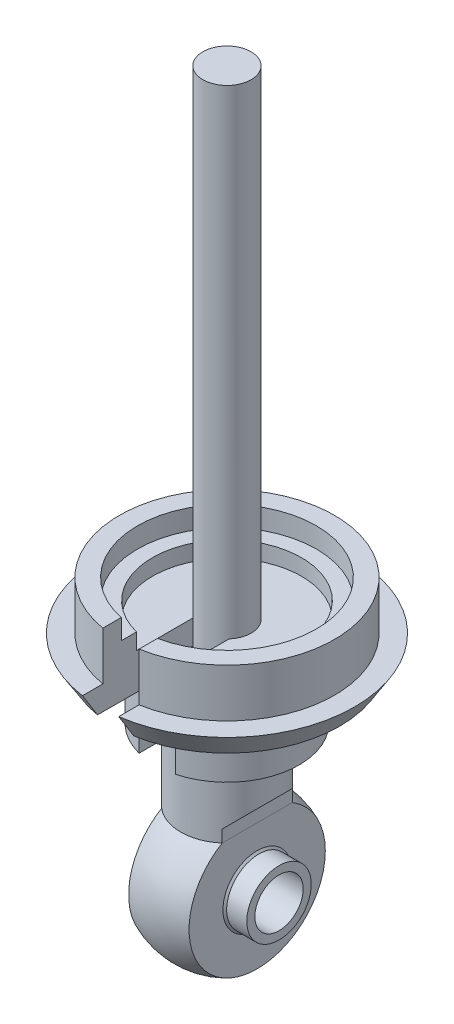
SolidWorks part; units mm, degrees
material "ABS PC"
ref_plane "Front Plane" through (0, 0, 0) normal (0, 0, 1) x (1, 0, 0)
ref_plane "Top Plane" through (0, 0, 0) normal (0, 1, 0) x (1, 0, 0)
ref_plane "Right Plane" through (0, 0, 0) normal (1, 0, 0) x (0, 0, -1)
sketch "Sketch1" plane through (0, 0, 0) normal (1, 0, 0) x (0, 0, -1)
  line L0 (0, 44) -> (0, -44) construction
  line L1 (-2.875, -30.625) -> (2.875, -30.625)
  line L2 (-2.875, -30.625) -> (-2.875, -40.3772)
  line L3 (2.875, -30.625) -> (2.875, -40.3772)
  line L4 (-2.875, -39.625) -> (2.875, -39.625)
  line L5 (-6.3918, -8.2) -> (6.3918, -8.2) construction
  line L6 (-1.5, -30.625) -> (-1.5, -0.625)
  line L7 (-1.5, -0.625) -> (1.5, -0.625)
  line L8 (-4.3, 44) -> (-4.3, 38.5)
  line L9 (-4.3, 38.5) -> (4.3, 38.5)
  line L10 (4.3, 44) -> (4.3, 38.5)
  line L11 (1.5, -0.625) -> (1.5, -30.625)
  line L12 (-7, 37.8) -> (7, 37.8)
  line L13 (-7, 37.8) -> (-7, 30.3)
  line L14 (-7, 30.3) -> (7, 30.3)
  line L15 (7, 30.3) -> (7, 37.8)
  line L16 (5.975, 30.3) -> (5.975, 9.3)
  line L17 (5.975, 9.3) -> (-5.975, 9.3)
  line L18 (5.05, 10.8) -> (5.9, 11.3)
  line L19 (5.05, 10.8) -> (5.05, 6.95)
  line L20 (5.05, 6.95) -> (4.5, -8.2)
  line L21 (4.5, -8.2) -> (-4.5, -8.2)
  line L22 (5.9, 11.3) -> (-5.9, 11.3)
  line L23 (5.9, 9.3) -> (5.9, 11.3)
  line L24 (5.05, 10.8) -> (-5.05, 10.8)
  line L25 (5.05, 6.95) -> (-5.05, 6.95)
  line L26 (-4.3, 38.5) -> (4.3, 38.5)
  line L27 (-4.3, 38.5) -> (-4.3, 37.8)
  line L28 (4.3, 38.5) -> (4.3, 37.8)
  line L29 (-5.975, 30.3) -> (-5.975, 9.3)
  line L30 (-5.9, 9.3) -> (-5.9, 11.3)
  line L31 (-5.05, 10.8) -> (-5.9, 11.3)
  line L32 (-5.05, 10.8) -> (-5.05, 6.95)
  line L33 (-5.05, 6.95) -> (-4.5, -8.2)
  line L34 (-8.35, 30.3) -> (8.35, 30.3)
  line L35 (8.475, 30.175) -> (8.475, 27.425)
  line L36 (8.35, 27.3) -> (6.9, 27.3)
  line L37 (6.9, 27.3) -> (6.9, 24.85)
  line L38 (-8.35, 30.3) -> (-8.475, 30.175)
  line L39 (6.9, 24.85) -> (-6.9, 24.85)
  line L40 (8.35, 30.3) -> (8.475, 30.175)
  line L41 (8.475, 27.425) -> (8.35, 27.3)
  line L42 (-8.475, 30.175) -> (-8.475, 27.425)
  line L43 (-8.475, 27.425) -> (-8.35, 27.3)
  line L44 (-8.35, 27.3) -> (-6.9, 27.3)
  line L45 (-6.9, 27.3) -> (-6.9, 24.85)
  circle A0 centre (0, 44) radius 2.5
  circle A1 centre (0, -44) radius 1.5
  circle A2 centre (0, -44) radius 2.1
  circle A3 centre (0, -44) radius 4.625
  circle A4 centre (0, -44) radius 4
  arc A5 (4.3, 44) -> (-4.3, 44) centre (0, 44) ccw
  point P9 (0, -30.625)
  point P12 (0, -48.625)
  point P23 (0, 48.3)
  point P25 (0, -0.625)
  point P28 (0, -8.2)
  point P31 (0, 37.8)
  point P44 (0, 10.8)
  point P46 (0, 41.5)
  point P51 (0, 9.3)
  point P54 (0, 11.3)
  point P55 (0, 6.95)
  point P56 (0, -8.2)
  point P57 (8.475, 30.3)
  point P58 (8.475, 27.3)
  point P68 (0, 30.3)
  point P72 (0, 24.85)
  line B0 (6.7, -28.34) -> (6.7, -30.7)
  line B1 (4.5, -36.21) -> (4.5, -32.03)
  line B2 (4.5, -32.03) -> (7.025, -32.03)
  line B3 (7.025, -32.03) -> (7.95, -30.7)
  line B4 (7.95, -30.7) -> (6.7, -30.7)
  line B5 (6.7, -28.34) -> (5.575, -28.34)
  line B6 (5.575, -28.34) -> (5.575, -29.59)
  line B7 (5.575, -29.59) -> (4.65, -29.59)
  line B8 (4.65, -29.59) -> (4.65, -30.59)
  line B9 (4.65, -30.59) -> (1.525, -30.59)
  line B10 (1.525, -30.59) -> (1.525, -32.21)
  line B11 (4.5, -36.21) -> (2.975, -36.21)
  line B12 (2.975, -36.21) -> (2.975, -32.21)
  line B13 (2.975, -32.21) -> (1.525, -32.21)
  dimension "D2" = 5
  dimension "D3" = 3
  dimension "D4" = 0.6
  dimension "D5" = 9.25
  dimension "D9" = 8
  dimension "D1" = 88
  dimension "D6" = 5.75
  dimension "D7" = 18
  dimension "D8" = 9
  dimension "D10" = 8.6
  dimension "D11" = 9.8
  dimension "D12" = 30
  dimension "D13" = 3
  dimension "D14" = 46
  dimension "D15" = 0.7
  dimension "D16" = 14
  dimension "D17" = 7.5
  dimension "D18" = 11.95
  dimension "D19" = 21
  dimension "D20" = 10.1
  dimension "D21" = 0.5
  dimension "D22" = 3.85
  dimension "D23" = 11.8
  dimension "D24" = 4.5
  dimension "D25" = 27
  dimension "D26" = 3
  dimension "D27" = 13.8
  dimension "D28" = 5.45
  dimension "D29" = 13.7
  dimension "D30" = 16.95
  dimension "D31" = 58
  dimension "D32" = 15.9
sketch_block_instance "Block1-1"
sketch_block "Block1"
sketch "Sketch2" plane through (0, 0, 0) normal (1, 0, 0) x (0, 0, -1)
  line L0 (0, -0.625) -> (1.5, -0.625)
  line L1 (-1.5, -0.625) -> (1.5, -0.625) construction
  line L2 (1.5, -0.625) -> (1.5, -30.625)
  line L3 (1.5, -30.625) -> (2.875, -30.625)
  line L4 (2.875, -30.625) -> (2.875, -40.3772)
  line L5 (2.875, -40.3772) -> (0, -40.3772)
  line L6 (0, 44) -> (0, -44) construction
  line L7 (0, -44) -> (0, 0) construction
  line L8 (0, -0.625) -> (0, -40.3772)
revolve "Revolve1" add sketch "Sketch2" angle 360 about L7
sketch "Sketch3" plane through (0, 0, 0) normal (0, 0, 1) x (1, 0, 0)
  line L0 (9.8663, -44) -> (-9.8663, -44) construction
  line L1 (0, -42.5) -> (-3.23, -42.5)
  line L2 (0, -45.5) -> (0, -42.5) construction
  line L3 (0, -46.1) -> (0, -41.9) construction
  line L4 (0, -42) -> (-3.23, -42)
  line L5 (0, -48) -> (0, -40) construction
  line L6 (0, -43.6961) -> (0, -52.6354) construction
  line L7 (0, -30.625) -> (0, -40.3772) construction
  line L8 (0, -48.625) -> (0, -39.375) construction
  line L9 (0, -42) -> (3.23, -42)
  line L10 (-3.23, -42) -> (-3.23, -42.5)
  line L11 (3.23, -42) -> (3.23, -42.5)
  line L12 (3.23, -42.5) -> (0, -42.5)
  line L13 (1.875, -39.7721) -> (1.875, -41.8727)
  line L14 (-1.875, -39.7721) -> (-1.875, -41.8727)
  arc A0 (1.875, -39.7721) -> (-1.875, -39.7721) centre (0, -44) ccw
  arc A1 (1.98, -42) -> (-1.98, -42) centre (0, -43.5263) ccw
  dimension "D5" = 2.5
  dimension "D1" = 6.46
  dimension "D2" = 3
  dimension "D3" = 4
  dimension "D4" = 1.25
  dimension "D6" = 3.75
revolve "Spherical Bearing" add sketch "Sketch3" angle 360 about L0
sketch "Sketch4" plane through (0, 0, 0) normal (0, 0, 1) x (1, 0, 0)
  line L0 (1.875, -39.625) -> (2.875, -39.625) construction
  line L2 (-3.23, -44) -> (3.23, -44) construction
  line L3 (-3.23, -42) -> (-3.23, -46) construction
  line L4 (3.23, -46) -> (3.23, -42) construction
  line L5 (2.875, -30.625) -> (-2.875, -30.625) construction
  line L6 (1.875, -47.6257) -> (1.875, -39.625)
  line L7 (1.875, -48.2279) -> (1.875, -39.7721) construction
  line L9 (1.875, -39.625) -> (2.875, -38.625)
  line L10 (2.875, -40.3772) -> (2.875, -30.625) construction
  line L11 (2.875, -38.625) -> (2.875, -47.6257)
  line L12 (2.875, -47.6257) -> (1.875, -47.6257)
  line L13 (0, -44) -> (0, -45.625) construction
  line L14 (0, -30.625) -> (0, -40.3772) construction
  line L15 (-1.875, -39.625) -> (-2.875, -38.625)
  line L16 (-1.875, -47.6257) -> (-1.875, -39.625)
  line L17 (-2.875, -47.6257) -> (-1.875, -47.6257)
  line L18 (-2.875, -38.625) -> (-2.875, -47.6257)
  dimension "D1" = 9
  dimension "D2" = 1
extrude "Cut-Extrude1" cut sketch "Sketch4" against normal mid plane 10
sketch "Sketch5" plane through (0, 0, 0) normal (1, 0, 0) x (0, 0, -1)
  line L0 (0, -28.1242) -> (6.675, -28.1242) construction
  line L1 (6.675, -28.1242) -> (6.675, -35.25) construction
  line L2 (6.675, -35.25) -> (-0.7895, -35.25) construction
  line L3 (-1.5, -0.625) -> (1.5, -0.625) construction
  line L4 (0, -44) -> (0, -25.5495) construction
  line L5 (6.675, -28.1242) -> (6.675, -31.1242)
  line L6 (4.475, -35.9742) -> (4.475, -32.6242)
  line L7 (4.475, -32.6242) -> (7, -32.6242)
  line L8 (7, -32.6242) -> (7.925, -31.1242)
  line L9 (7.925, -31.1242) -> (6.675, -31.1242)
  line L10 (6.675, -28.1242) -> (5.55, -28.1242)
  line L11 (5.55, -28.1242) -> (5.55, -29.3742)
  line L12 (5.55, -29.3742) -> (4.625, -29.3742)
  line L13 (4.625, -29.3742) -> (4.625, -30.3742)
  line L14 (4.625, -30.3742) -> (1.5, -30.3742)
  line L15 (0, -44) -> (0, -48.6242)
  line L16 (4.475, -35.9742) -> (2.95, -35.9742)
  line L17 (2.95, -35.9742) -> (2.95, -31.7579)
  line L18 (2.95, -31.7579) -> (1.5, -31.7579)
  line L21 (1.5, -30.3742) -> (1.5, -31.7579)
  dimension "D2" = 20.5
  dimension "D3" = 1.5
  dimension "D4" = 13.35
  dimension "D5" = 15.85
  dimension "D6" = 14
  dimension "D7" = 11.1
  dimension "D8" = 5.9
  dimension "D9" = 1.25
  dimension "D10" = 2.25
  dimension "D11" = 7.85
  dimension "D12" = 9.25
  dimension "D13" = 8.95
  dimension "D15" = 3
revolve "Revolve3" add sketch "Sketch5" angle 360 about L4
sketch "Sketch6" plane through (0, -30.3742, 0) normal (0, 1, 0) x (1, 0, 0)
  line L0 (0, 0) -> (0, -7.925) construction
  line L2 (-1.125, -0.9922) -> (1.125, -0.9922) construction
  line L3 (-1.125, -0.9922) -> (-1.125, -8.7437)
  line L4 (-1.125, -8.7437) -> (1.125, -8.7437)
  line L5 (1.125, -0.9922) -> (1.125, -8.7437)
  circle A0 centre (0, 0) radius 7.925 construction
  circle A1 centre (0, 0) radius 1.5 construction
  circle A2 centre (0, 0) radius 1.5 construction
  arc A3 (-1.125, -0.9922) -> (1.125, -0.9922) centre (0, 0) ccw
  dimension "D1" = 2.25
extrude "Cut-Extrude2" cut sketch "Sketch6" against normal blind 1.51 and the other way blind 3
sketch "Sketch7" plane through (0, -31.8842, 0) normal (0, 1, 0) x (1, 0, 0)
  line L0 (-1.125, -4.3313) -> (-1.125, -2.7271)
  line L1 (1.125, -4.3313) -> (1.125, -2.7271)
  line L3 (-1.125, -0.9922) -> (-1.125, -8.7437)
  line L4 (-1.125, -8.7437) -> (1.125, -8.7437)
  line L5 (1.125, -8.7437) -> (1.125, -0.9922)
  line L6 (-1.125, -4.3313) -> (-1.125, -8.7437)
  line L7 (-1.125, -8.7437) -> (1.125, -8.7437)
  line L8 (1.125, -8.7437) -> (1.125, -4.3313)
  arc A1 (-1.125, -0.9922) -> (1.125, -0.9922) centre (0, 0) ccw
  circle A2 centre (0, 0) radius 2.95 construction
  arc A4 (-1.125, -2.7271) -> (1.125, -2.7271) centre (0, 0) ccw
  dimension "D1" = 0
extrude "Cut-Extrude3" cut sketch "Sketch7" against normal blind 6
ref_point "Point1"
